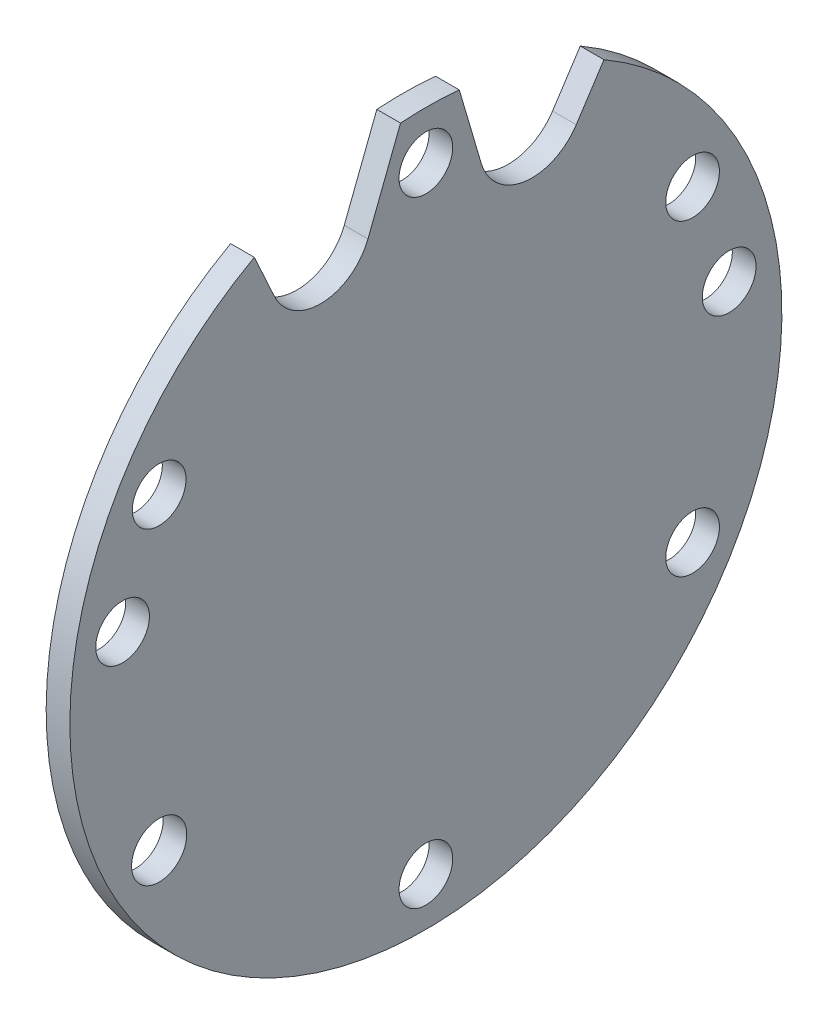
SolidWorks part; units mm, degrees
ref_plane "Front Plane" through (0, 0, 0) normal (0, 0, 1) x (1, 0, 0)
ref_plane "Top Plane" through (0, 0, 0) normal (0, 1, 0) x (1, 0, 0)
ref_plane "Right Plane" through (0, 0, 0) normal (1, 0, 0) x (0, 0, -1)
sketch "Sketch1" plane through (0, 0, 0) normal (1, 0, 0) x (0, 0, -1)
  line L0 (-21.7247, 39.5056) -> (-19.1946, 33.9711)
  line L1 (-7.3346, 34.3229) -> (-3.2112, 44.9705)
  line L2 (4.2332, 44.8858) -> (7.0168, 35.4278)
  line L3 (22.5518, 39.0394) -> (19.0425, 33.6604)
  arc A0 (-21.7247, 39.5056) -> (22.5518, 39.0394) centre (0, 0) ccw
  circle A1 centre (0, 39) radius 3.4
  circle A2 centre (33.775, 19.5) radius 3.4
  circle A3 centre (38.4075, 6.7723) radius 3.4
  circle A4 centre (33.775, -19.5) radius 3.4
  circle A5 centre (0, -39) radius 3.4
  circle A6 centre (-33.775, -19.5) radius 3.4929
  circle A7 centre (-38.4075, 6.7723) radius 3.4
  circle A8 centre (-33.775, 19.5) radius 3.4
  arc A10 (-19.1946, 33.9711) -> (-7.3346, 34.3229) centre (-13.3388, 36.648) ccw
  arc A12 (7.0168, 35.4278) -> (19.0425, 33.6604) centre (13.4372, 37.3174) ccw
  arc A13 (4.2332, 44.8858) -> (-3.2112, 44.9705) centre (0, 0) ccw
  dimension "D1" = 90.17
extrude "Boss-Extrude1" add sketch "Sketch1" along normal blind 3
